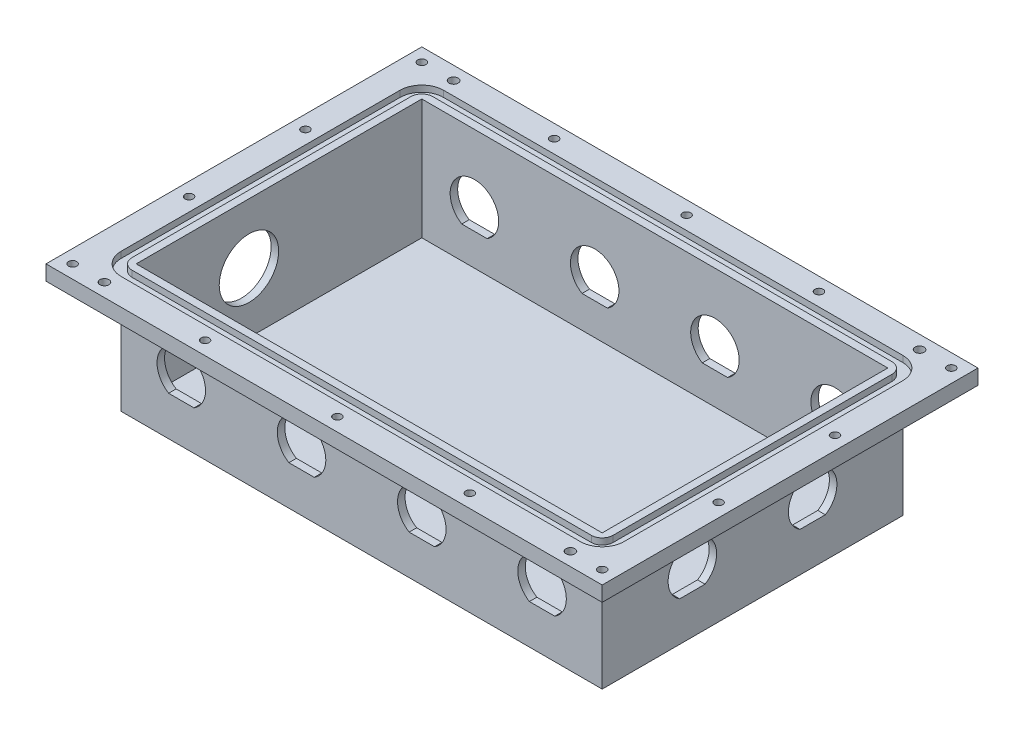
SolidWorks part; units mm, degrees
material "1060 Alloy"
ref_plane "Front Plane" through (0, 0, 0) normal (0, 0, 1) x (1, 0, 0)
ref_plane "Top Plane" through (0, 0, 0) normal (0, 1, 0) x (1, 0, 0)
ref_plane "Right Plane" through (0, 0, 0) normal (1, 0, 0) x (0, 0, -1)
sketch "Sketch1" plane through (0, 0, 0) normal (0, 1, 0) x (1, 0, 0)
  line L1 (101.6, -63.5) -> (-101.6, -63.5)
  line L2 (101.6, -63.5) -> (101.6, 63.5)
  line L3 (101.6, 63.5) -> (-101.6, 63.5)
  line L4 (-101.6, -63.5) -> (-101.6, 63.5)
  line L5 (101.6, -63.5) -> (-101.6, 63.5) construction
  line L6 (101.6, 63.5) -> (-101.6, -63.5) construction
  point P0 (0, 0)
  dimension "D1" = 127
  dimension "D2" = 203.2
extrude "Boss-Extrude1" add sketch "Sketch1" along normal blind 53.975
sketch "Sketch2" plane through (0, 53.975, 0) normal (0, 1, 0) x (1, 0, 0)
  line L8 (-98.425, 60.325) -> (-98.425, -60.325)
  line L9 (98.425, 60.325) -> (-98.425, 60.325)
  line L10 (98.425, -60.325) -> (98.425, 60.325)
  line L11 (-98.425, -60.325) -> (98.425, -60.325)
  line L12 (-98.425, 60.325) -> (-98.425, -60.325)
  line L13 (98.425, 60.325) -> (-98.425, 60.325)
  line L14 (98.425, -60.325) -> (98.425, 60.325)
  line L15 (-98.425, -60.325) -> (98.425, -60.325)
  dimension "D1" = 3.175
extrude "Cut-Extrude1" cut sketch "Sketch2" against normal offset from surface (50.8 mm away) 3.175 up to face at (0, 0, 0)
sketch "Sketch4" plane through (0, 53.975, 0) normal (0, 1, 0) x (1, 0, 0)
  line L0 (-101.6, 63.5) -> (-101.6, -63.5)
  line L1 (-101.6, -63.5) -> (101.6, -63.5)
  line L2 (101.6, -63.5) -> (101.6, 63.5)
  line L3 (101.6, 63.5) -> (-101.6, 63.5)
  line L4 (117.475, 79.375) -> (-117.475, 79.375)
  line L5 (-117.475, 79.375) -> (-117.475, -79.375)
  line L6 (-117.475, -79.375) -> (117.475, -79.375)
  line L7 (117.475, -79.375) -> (117.475, 79.375)
  dimension "D1" = 15.875
extrude "Boss-Extrude2" add sketch "Sketch4" against normal blind 6.35
sketch "Sketch7" plane through (0, 53.975, 0) normal (0, 1, 0) x (1, 0, 0)
  line L4 (-106.2228, 68.1228) -> (-106.2228, -68.1228)
  line L5 (-106.2228, -68.1228) -> (106.2228, -68.1228)
  line L6 (106.2228, -68.1228) -> (106.2228, 68.1228)
  line L7 (106.2228, 68.1228) -> (-106.2228, 68.1228)
  line L8 (-101.6, -63.5) -> (101.6, -63.5)
  line L9 (101.6, -63.5) -> (101.6, 63.5)
  line L10 (101.6, 63.5) -> (-101.6, 63.5)
  line L11 (-101.6, 63.5) -> (-101.6, -63.5)
  line L12 (-101.6, -63.5) -> (101.6, -63.5)
  line L13 (101.6, -63.5) -> (101.6, 63.5)
  line L14 (101.6, 63.5) -> (-101.6, 63.5)
  line L15 (-101.6, 63.5) -> (-101.6, -63.5)
  dimension "D1" = 3.175
  dimension "D2" = 4.6228
extrude "Cut-Extrude2" cut sketch "Sketch7" against normal blind 2.6416
hole_wizard "#8-32 Tapped Hole1" positions "Sketch6" profile "Sketch5" tap size "#8-32" standard "ANSI Inch" end condition through all
sketch "Sketch6" plane through (0, 53.975, 0) normal (0, 1, 0) x (1, 0, 0)
  line L0 (0, 0) -> (0, 79.375) construction
  line L1 (117.475, 79.375) -> (-117.475, 79.375) construction
  line L4 (0, 0) -> (117.475, 0) construction
  line L5 (117.475, -79.375) -> (117.475, 79.375) construction
  line L6 (0, 73.7489) -> (55.9244, 73.7489) construction
  line L7 (55.9244, 73.7489) -> (111.8489, 73.7489) construction
  line L10 (111.8489, 73.7489) -> (111.8489, 24.583) construction
  line L13 (111.8489, 24.583) -> (111.8489, -24.583) construction
  line L16 (106.2228, 68.1228) -> (117.475, 79.375) construction
  point P22 (55.9244, 73.7489)
  point P24 (111.8489, 73.7489)
  point P26 (111.8489, 24.583)
  point P110 (0, 73.7489)
  point P132 (111.8489, -24.583)
  point P133 (111.8489, -73.7489)
  point P134 (55.9244, -73.7489)
  point P135 (0, -73.7489)
  point P145 (-55.9244, -73.7489)
  point P146 (-111.8489, -73.7489)
  point P147 (-111.8489, -24.583)
  point P148 (-111.8489, 24.583)
  point P149 (-111.8489, 73.7489)
  point P150 (-55.9244, 73.7489)
sketch "Sketch5" plane through (55.9244, 53.975, -73.7489) normal (1, 0, 0) x (0, 0, 1)
  line L0 (0, 0) -> (0, 53.975)
  line L1 (0, 53.975) -> (1.7272, 53.975)
  line L2 (1.7272, 53.975) -> (1.7272, 0)
  line L5 (1.7272, 0) -> (0, 0)
  line L11 (0, -6.35) -> (0, 107.95) construction
  dimension "Thread Major Dia." = 3.4544
  dimension "Thru Tap Drill Depth" = 53.975
sketch "O Ring Corner Fillet Dimentions" plane through (0, 53.975, 0) normal (0, 1, 0) x (1, 0, 0)
  line L0 (106.2228, 68.1228) -> (96.9772, 58.8772) construction
  line L1 (106.2228, 68.1228) -> (-106.2228, 68.1228) construction
  line L2 (106.2228, -68.1228) -> (106.2228, 68.1228) construction
  circle A0 centre (96.9772, 58.8772) radius 9.2456
  circle A1 centre (96.9772, 58.8772) radius 4.6228
  dimension "D1" = 4.6228
  dimension "D2" = 18.4912
  dimension "D3" = 9.2456
fillet "Fillet3" radius 4.6228 4 edges at (101.6, 52.6542, 63.5) (-101.6, 52.6542, 63.5) (-101.6, 52.6542, -63.5) (101.6, 52.6542, -63.5)
fillet "Fillet4" radius 9.2456 4 edges at (106.2228, 52.6542, 68.1228) (-106.2228, 52.6542, 68.1228) (-106.2228, 52.6542, -68.1228) (106.2228, 52.6542, -68.1228)
sketch "Sketch10" plane through (0, 0, 63.5) normal (0, 0, 1) x (1, 0, 0)
  line L0 (0, 25.4) -> (50.8, 25.4) construction
  line L1 (-101.6, 0) -> (101.6, 0) construction
  line L3 (-104.775, 16.6624) -> (104.775, 16.6624)
  line L4 (0, 25.4) -> (0, 47.625) construction
  line L5 (-101.6, 47.625) -> (101.6, 47.625) construction
  line L6 (50.8, 25.4) -> (101.6, 25.4) construction
  line L7 (101.6, 47.625) -> (101.6, 0) construction
  line L8 (0, 25.4) -> (-50.8, 25.4) construction
  line L9 (-50.8, 25.4) -> (-101.6, 25.4) construction
  line L10 (-101.6, 47.625) -> (-101.6, 0) construction
  circle A0 centre (-76.2, 25.4) radius 10.2489
  circle A1 centre (-25.4, 25.4) radius 10.2489
  circle A2 centre (25.4, 25.4) radius 10.2489
  circle A3 centre (76.2, 25.4) radius 10.2489
  point P5 (-76.2, 25.4)
  point P9 (-25.4, 25.4)
  point P12 (25.4, 25.4)
  point P13 (76.2, 25.4)
  dimension "D2" = 25.4
  dimension "D1" = 20.4978
  dimension "D3" = 8.7376
extrude "Cut-Extrude5" cut sketch "Sketch10" against normal through all
sketch "Sketch12" plane through (101.6, 0, 0) normal (1, 0, 0) x (0, 0, -1)
  line L0 (63.5, 25.4) -> (-63.5, 25.4) construction
  line L1 (63.5, 47.625) -> (63.5, 0) construction
  line L2 (-63.5, 47.625) -> (-63.5, 0) construction
  line L4 (-63.5, 16.6624) -> (63.5, 16.6624)
  circle A0 centre (-25.4, 25.4) radius 10.2489
  circle A1 centre (25.4, 25.4) radius 10.2489
  point P6 (63.5, 25.4)
  point P7 (-25.4, 25.4)
  point P10 (25.4, 25.4)
  dimension "D2" = 8.7376
  dimension "D3" = 20.4978
  dimension "D1" = 38.1
  dimension "D4" = 38.1
extrude "Cut-Extrude6" cut sketch "Sketch12" against normal up to next
sketch "Sketch13" plane through (-101.6, 0, 0) normal (-1, 0, 0) x (0, 0, 1)
  line L0 (63.5, 23.8125) -> (-63.5, 23.8125) construction
  line L1 (63.5, 47.625) -> (63.5, 0) construction
  line L2 (-63.5, 47.625) -> (-63.5, 0) construction
  line L3 (-63.5, 47.625) -> (63.5, 47.625) construction
  circle A0 centre (12.7, 28.575) radius 12.554
  point P6 (25.4, 23.8125)
  point P7 (12.7, 28.575)
  dimension "D3" = 25.1079
  dimension "D4" = 19.05
  dimension "D5" = 19.05
  dimension "D1" = 38.1
  dimension "D2" = 76.2
extrude "Cut-Extrude7" cut sketch "Sketch13" against normal up to next
hole_wizard "#6 Clearance Hole1" positions "Sketch15" profile "Sketch14" hole size "#6" standard "ANSI Inch" end condition through all
sketch "Sketch15" plane through (0, 47.625, 0) normal (0, -1, 0) x (-1, 0, 0)
  line L0 (-101.6, -63.5) -> (-101.6, 63.5) construction
  line L1 (0, 0) -> (0, 87.6055) construction
  line L4 (0, 0) -> (66.1414, 0) construction
  line L7 (-111.8489, 73.7489) -> (-55.9244, 73.7489) construction
  point P2 (-98.425, 73.7489)
  point P31 (-98.425, -73.7489)
  point P32 (98.425, -73.7489)
  point P33 (98.425, 73.7489)
  dimension "D1" = 3.175
sketch "Sketch14" plane through (98.425, 47.625, -73.7489) normal (1, 0, 0) x (0, 0, -1)
  line L0 (0, 0) -> (0, 6.35)
  line L1 (0, 6.35) -> (1.8986, 6.35)
  line L2 (1.8986, 6.35) -> (1.8986, 0)
  line L5 (1.8986, 0) -> (0, 0)
  line L11 (0, -6.35) -> (0, 107.95) construction
  dimension "Thru Hole Dia." = 3.7973
  dimension "Thru Hole Depth" = 6.35
